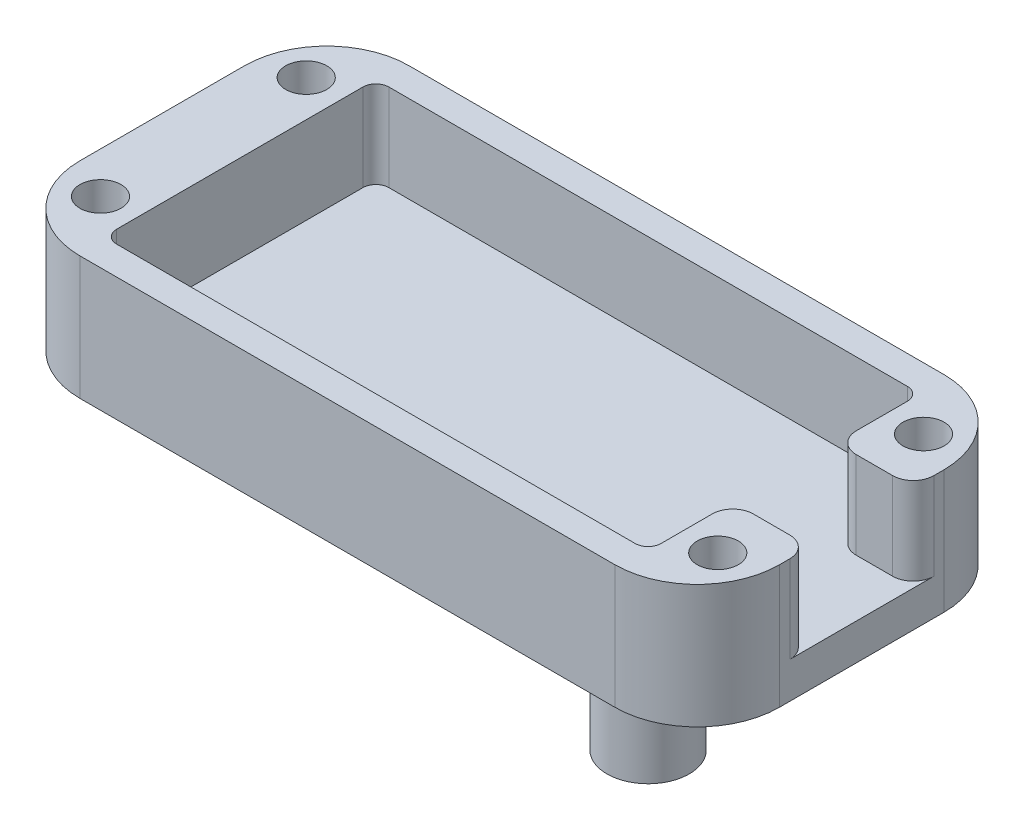
SolidWorks part; units mm, degrees
ref_plane "Front Plane" through (0, 0, 0) normal (0, 0, 1) x (1, 0, 0)
ref_plane "Top Plane" through (0, 0, 0) normal (0, 1, 0) x (1, 0, 0)
ref_plane "Right Plane" through (0, 0, 0) normal (1, 0, 0) x (0, 0, -1)
sketch "Sketch1" plane through (0, 0, 0) normal (0, 1, 0) x (1, 0, 0)
  line L1 (0, 0) -> (53.975, 0)
  line L2 (0, 0) -> (0, 25.4)
  line L3 (0, 25.4) -> (53.975, 25.4)
  line L4 (53.975, 0) -> (53.975, 25.4)
  dimension "D1" = 53.975
  dimension "D2" = 25.4
extrude "Boss-Extrude1" add sketch "Sketch1" along normal blind 9.525
sketch "Sketch2" plane through (0, 9.525, 0) normal (0, 1, 0) x (1, 0, 0)
  line L0 (53.975, 0) -> (53.975, 25.4) construction
  line L1 (5.9875, 23.2) -> (47.9875, 23.2)
  line L2 (5.9875, 23.2) -> (5.9875, 2.2)
  line L3 (5.9875, 2.2) -> (47.9875, 2.2)
  line L4 (47.9875, 23.2) -> (47.9875, 2.2)
  line L5 (53.975, 25.4) -> (0, 25.4) construction
  line L6 (53.975, 0) -> (53.975, 25.4) construction
  line L7 (53.975, 25.4) -> (0, 25.4) construction
  point P6 (26.9875, 23.2)
  point P8 (26.9875, 25.4)
  point P9 (53.975, 12.7)
  point P10 (47.9875, 12.7)
  dimension "D1" = 42
  dimension "D2" = 21
extrude "Cut-Extrude1" cut sketch "Sketch2" against normal blind 6.725
fillet "Fillet1" radius 1 4 edges at (5.9875, 6.1625, -2.2) (47.9875, 6.1625, -2.2) (5.9875, 6.1625, -23.2) (47.9875, 6.1625, -23.2)
sketch "Sketch3" plane through (0, 0, 0) normal (0, -1, 0) x (1, 0, 0)
  line L0 (6.9875, -2.2) -> (46.9875, -2.2) construction
  line L1 (47.9875, -3.2) -> (47.9875, -22.2) construction
  line L2 (46.9875, -23.2) -> (6.9875, -23.2) construction
  line L3 (6.9875, -2.2) -> (46.9875, -2.2) construction
  line L4 (47.9875, -3.2) -> (47.9875, -22.2) construction
  line L5 (46.9875, -23.2) -> (6.9875, -23.2) construction
  circle A0 centre (37.4875, -12.7) radius 10.5 construction
  circle A1 centre (37.4875, -12.7) radius 3.175
  dimension "D1" = 6.35
extrude "Boss-Extrude2" add sketch "Sketch3" along normal blind 14.2875
sketch "Sketch4" plane through (0, 9.525, 0) normal (0, 1, 0) x (1, 0, 0)
  line L0 (53.975, 0) -> (53.975, 25.4) construction
  line L1 (0, 25.4) -> (0, 0) construction
  line L2 (53.975, 0) -> (53.975, 25.4) construction
  line L3 (0, 25.4) -> (0, 0) construction
  line L4 (3.175, 20.6375) -> (3.175, 4.7625) construction
  line L5 (50.8, 20.6375) -> (50.8, 4.7625) construction
  circle A0 centre (3.175, 20.6375) radius 1.5875
  circle A1 centre (3.175, 4.7625) radius 1.5875
  circle A2 centre (50.8, 20.6375) radius 1.5875
  circle A3 centre (50.8, 4.7625) radius 1.5875
  point P8 (0, 12.7)
  point P9 (3.175, 12.7)
  point P10 (50.8, 12.7)
  point P11 (53.975, 12.7)
  dimension "D4" = 3.175
  dimension "D1" = 3.175
  dimension "D2" = 3.175
  dimension "D3" = 15.875
extrude "Cut-Extrude2" cut sketch "Sketch4" against normal up to surface (9.525 mm away) up to face at (37.4875, 0, -15.875)
fillet "Fillet2" radius 6.35 4 edges at (53.975, 4.7625, 0) (53.975, 4.7625, -25.4) (0, 4.7625, -25.4) (0, 4.7625, 0)
sketch "Sketch5" plane through (0, 9.525, 0) normal (0, 1, 0) x (1, 0, 0)
  line L0 (53.975, 6.35) -> (53.975, 19.05) construction
  line L1 (53.975, 6.35) -> (53.975, 19.05) construction
  line L3 (47.9875, 16.6687) -> (53.975, 16.6687)
  line L4 (53.975, 8.7312) -> (53.975, 16.6687)
  line L5 (47.9875, 16.6687) -> (47.9875, 8.7312)
  line L6 (53.975, 8.7312) -> (47.9875, 8.7312)
  line L7 (47.9875, 3.2) -> (47.9875, 22.2) construction
  line L8 (47.9875, 3.2) -> (47.9875, 22.2) construction
  point P2 (47.9875, 12.7)
  point P9 (53.975, 12.7)
  point P10 (53.975, 12.7)
  dimension "D1" = 7.9375
extrude "Cut-Extrude3" cut sketch "Sketch5" against normal up to surface (6.725 mm away) up to face at (26.9875, 2.8, -12.7)
fillet "Fillet3" radius 1.5875 4 edges at (47.9875, 6.1625, -16.6688) (47.9875, 6.1625, -8.7312) (53.975, 6.1625, -8.7312) (53.975, 6.1625, -16.6687)
